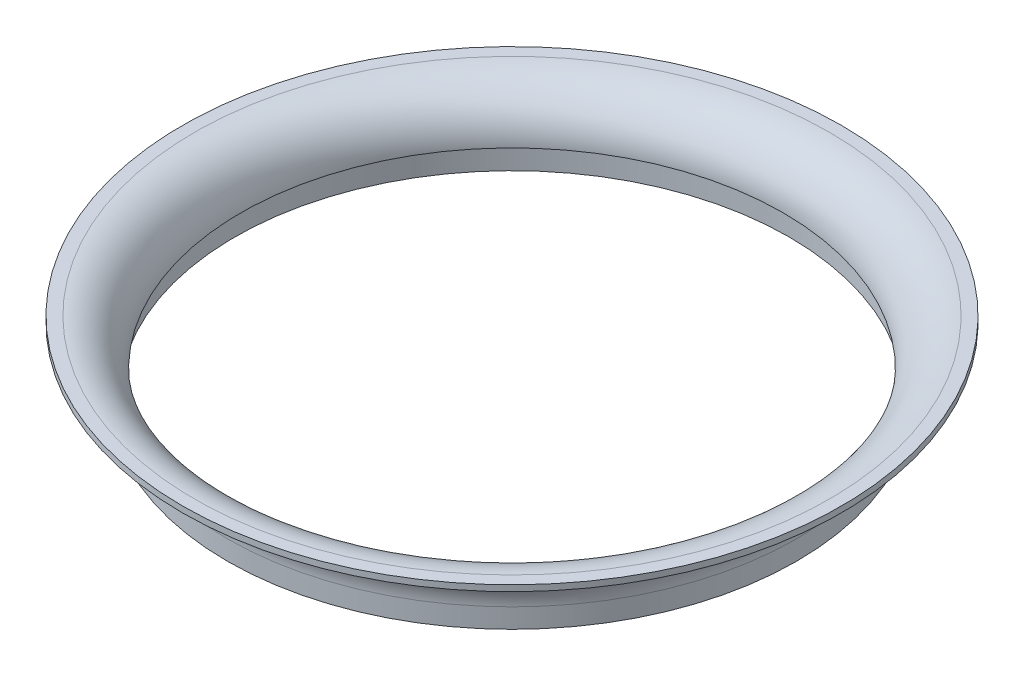
SolidWorks part; units mm, degrees
ref_plane "Front Plane" through (0, 0, 0) normal (0, 0, 1) x (1, 0, 0)
ref_plane "Top Plane" through (0, 0, 0) normal (0, 1, 0) x (1, 0, 0)
ref_plane "Right Plane" through (0, 0, 0) normal (1, 0, 0) x (0, 0, -1)
sketch "Sketch1" plane through (0, 0, 0) normal (0, 0, 1) x (1, 0, 0)
  line L0 (0, 0) -> (0, 39461.5541) construction
  line L1 (47.5, 0) -> (47.5, 3.25)
  line L2 (55, 10.75) -> (55, 11.75)
  line L3 (55, 11.75) -> (53, 11.75)
  line L4 (45.25, 4) -> (46.25, 4)
  line L5 (46.25, 4) -> (46.25, 0)
  line L6 (46.25, 0) -> (47.5, 0)
  line L7 (45.25, 4) -> (45.25, 3.0269) construction
  line L8 (55, 10.75) -> (57.7258, 10.75) construction
  arc A0 (47.5, 3.25) -> (55, 10.75) centre (55, 3.25) cw
  arc A1 (53, 11.75) -> (45.25, 4) centre (53, 4) ccw
  dimension "D1" = 47.5
  dimension "D2" = 46.25
  dimension "D3" = 45.25
  dimension "D4" = 4
  dimension "D5" = 2
  dimension "D6" = 55
  dimension "D7" = 1
revolve "Revolve1" add sketch "Sketch1" angle 360 about L0
